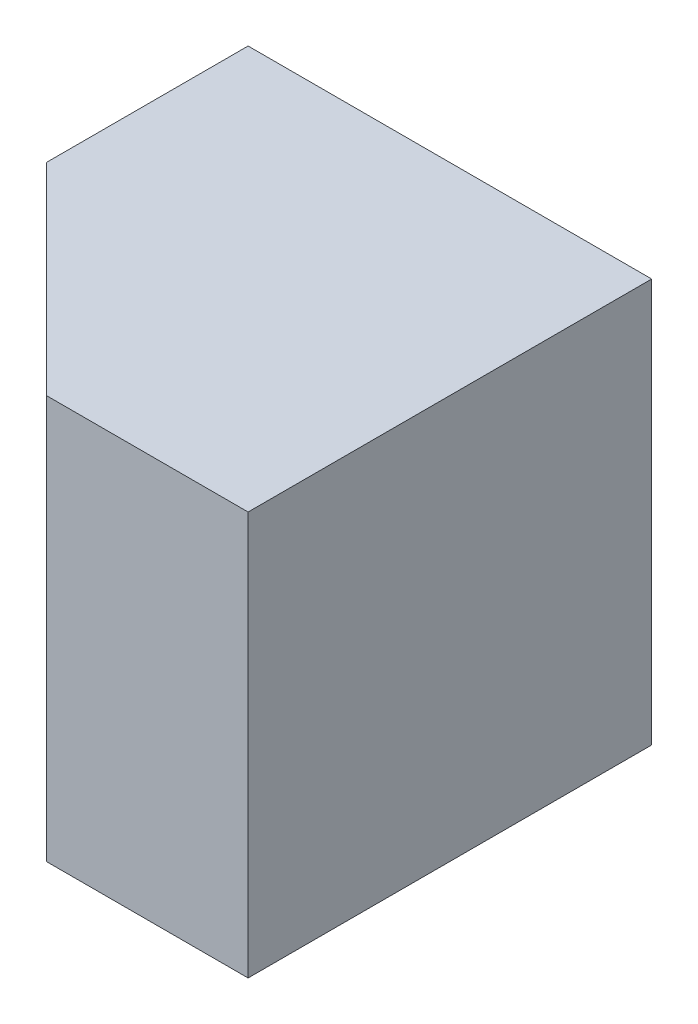
SolidWorks part; units mm, degrees
ref_plane "Front Plane" through (0, 0, 0) normal (0, 0, 1) x (1, 0, 0)
ref_plane "Top Plane" through (0, 0, 0) normal (0, 1, 0) x (1, 0, 0)
ref_plane "Right Plane" through (0, 0, 0) normal (1, 0, 0) x (0, 0, -1)
sketch "Sketch1" plane through (0, 0, 0) normal (0, 0, 1) x (1, 0, 0)
  line L1 (0, 0) -> (20, 0)
  line L2 (0, 0) -> (0, 20)
  line L3 (0, 20) -> (20, 20)
  line L4 (20, 0) -> (20, 20)
  dimension "D1" = 20
  dimension "D2" = 20
extrude "Boss-Extrude1" add sketch "Sketch1" along normal blind 20
sketch "Sketch2" plane through (0, 20, 0) normal (0, 1, 0) x (1, 0, 0)
  line L0 (0, -10) -> (10, -20)
  line L1 (0, -20) -> (0, 0) construction
  line L2 (20, -20) -> (0, -20) construction
  line L3 (10, -20) -> (0, -20)
  line L4 (0, -20) -> (0, -10)
extrude "Cut-Extrude1" cut sketch "Sketch2" against normal blind 20
